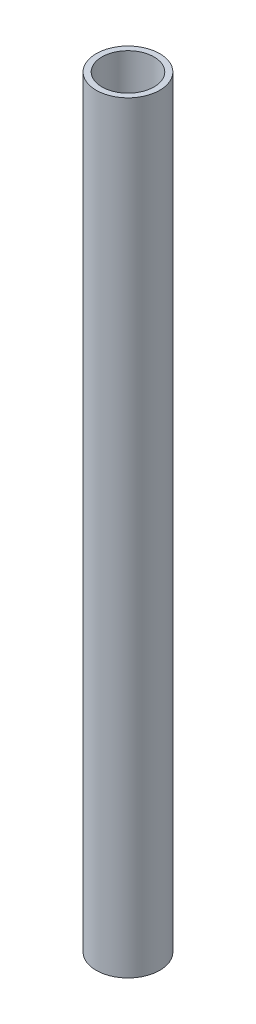
SolidWorks part; units mm, degrees
ref_plane "Front Plane" through (0, 0, 0) normal (0, 0, 1) x (1, 0, 0)
ref_plane "Top Plane" through (0, 0, 0) normal (0, 1, 0) x (1, 0, 0)
ref_plane "Right Plane" through (0, 0, 0) normal (1, 0, 0) x (0, 0, -1)
sketch "Sketch1" plane through (0, 0, 0) normal (0, 1, 0) x (1, 0, 0)
  circle A0 centre (0, 0) radius 12.7
  circle A1 centre (0, 0) radius 10.414
  dimension "D1" = 25.4
  dimension "D2" = 20.828
extrude "Boss-Extrude1" add sketch "Sketch1" along normal blind 304.8
